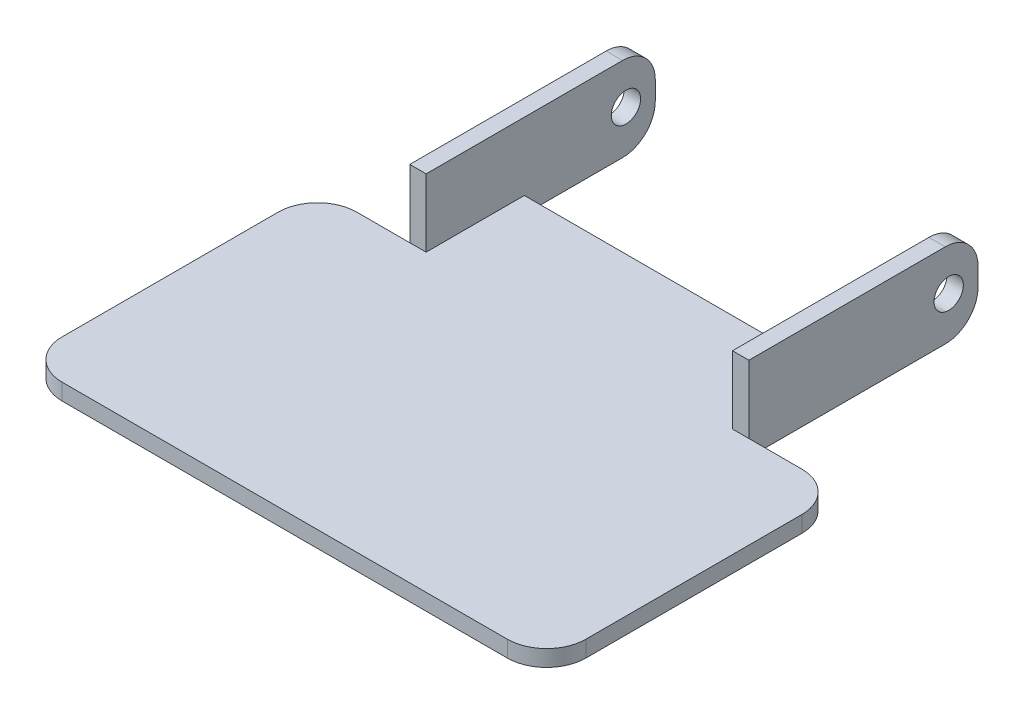
SolidWorks part; units mm, degrees
ref_plane "Front Plane" through (0, 0, 0) normal (0, 0, 1) x (1, 0, 0)
ref_plane "Top Plane" through (0, 0, 0) normal (0, 1, 0) x (1, 0, 0)
ref_plane "Right Plane" through (0, 0, 0) normal (1, 0, 0) x (0, 0, -1)
sketch "Sketch1" plane through (0, 0, 0) normal (0, 1, 0) x (1, 0, 0)
  line L0 (8.9535, 28.575) -> (8.9535, 50.8)
  line L1 (0, 0) -> (50.8, 0)
  line L2 (0, 0) -> (0, 28.575)
  line L3 (0, 28.575) -> (8.9535, 28.575)
  line L4 (50.8, 0) -> (50.8, 28.575)
  line L5 (8.9535, 50.8) -> (10.541, 50.8)
  line L6 (10.541, 50.8) -> (10.541, 38.1)
  line L7 (10.541, 38.1) -> (40.259, 38.1)
  line L8 (40.259, 38.1) -> (40.259, 50.8)
  line L9 (40.259, 50.8) -> (41.8465, 50.8)
  line L10 (41.8465, 50.8) -> (41.8465, 28.575)
  line L11 (41.8465, 28.575) -> (50.8, 28.575)
  dimension "D1" = 1.5875
  dimension "D2" = 50.8
  dimension "D3" = 28.575
  dimension "D4" = 38.1
  dimension "D5" = 32.893
  dimension "D6" = 50.8
extrude "Boss-Extrude1" add sketch "Sketch1" along normal blind 1.5875
sketch "Sketch2" plane through (0, 1.5875, 0) normal (0, 1, 0) x (1, 0, 0)
  line L1 (8.9535, 28.575) -> (10.541, 28.575)
  line L2 (8.9535, 28.575) -> (8.9535, 50.8)
  line L3 (8.9535, 50.8) -> (10.541, 50.8)
  line L4 (10.541, 28.575) -> (10.541, 50.8)
  line L5 (41.8465, 28.575) -> (40.259, 28.575)
  line L6 (41.8465, 28.575) -> (41.8465, 50.8)
  line L7 (41.8465, 50.8) -> (40.259, 50.8)
  line L8 (40.259, 28.575) -> (40.259, 50.8)
extrude "Boss-Extrude2" add sketch "Sketch2" along normal blind 6.5786
fillet "Fillet1" radius 3.175 4 edges at (41.0527, 8.1661, -50.8) (41.0527, 0, -50.8) (9.7472, 8.1661, -50.8) (9.7472, 0, -50.8)
fillet "Fillet2" radius 3.81 4 edges at (0, 0.7937, -28.575) (0, 0.7937, 0) (50.8, 0.7937, 0) (50.8, 0.7937, -28.575)
hole_wizard "Hole1" positions "Sketch4" profile "Sketch3" legacy end condition through all
sketch "Sketch4" plane through (8.9535, 0, 0) normal (-1, 0, 0) x (0, 0, 1)
  line L0 (-50.8, 4.0831) -> (-28.575, 4.083) construction
  line L1 (-50.8, 4.9911) -> (-50.8, 3.175) construction
  line L2 (-28.575, 8.1661) -> (-28.575, 1.5875) construction
  point P0 (-47.9552, 4.083)
  dimension "D1" = 2.8448
sketch "Sketch3" plane through (8.9535, 4.083, -47.9552) normal (0, 1, 0) x (0, 0, 1)
  line L0 (0, 0) -> (0, 41.8465)
  line L1 (0, 41.8465) -> (1.4224, 41.8465)
  line L2 (1.4224, 41.8465) -> (1.4224, 0)
  line L3 (1.4224, 0) -> (0, 0)
  line L4 (0, 110) -> (0, -10) construction
  dimension "Diameter" = 2.8448
  dimension "Depth" = 41.8465
